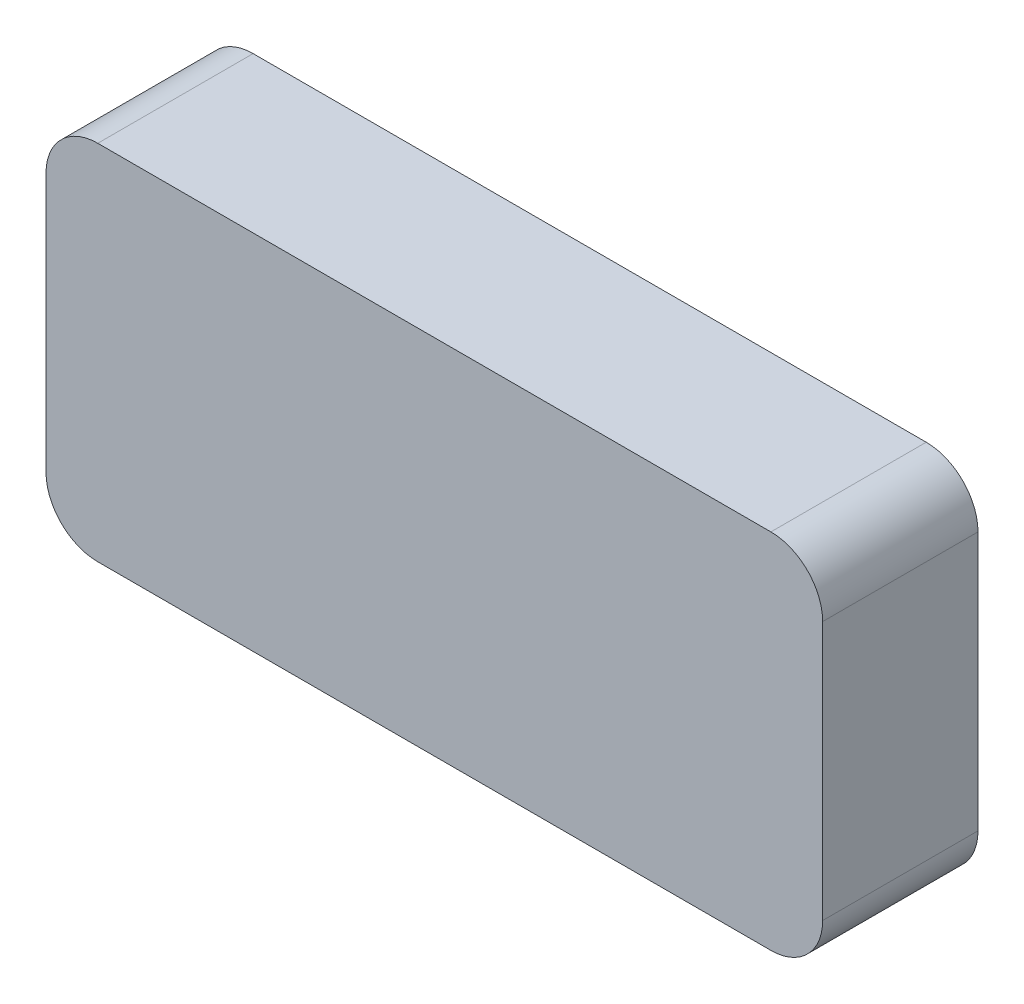
SolidWorks part; units mm, degrees
ref_plane "정면" through (0, 0, 0) normal (0, 0, 1) x (1, 0, 0)
ref_plane "윗면" through (0, 0, 0) normal (0, 1, 0) x (1, 0, 0)
ref_plane "우측면" through (0, 0, 0) normal (1, 0, 0) x (0, 0, -1)
sketch "스케치1" plane through (0, 0, 0) normal (0, 0, 1) x (1, 0, 0)
  line L1 (0, 0) -> (150, 0)
  line L2 (0, 0) -> (0, -70)
  line L3 (0, -70) -> (150, -70)
  line L4 (150, 0) -> (150, -70)
  dimension "D1" = 150
  dimension "D2" = 70
extrude "보스-돌출1" add sketch "스케치1" along normal blind 30
fillet "필렛1" radius 10 4 edges at (150, -70, 15) (0, -70, 15) (0, 0, 15) (150, 0, 15)
